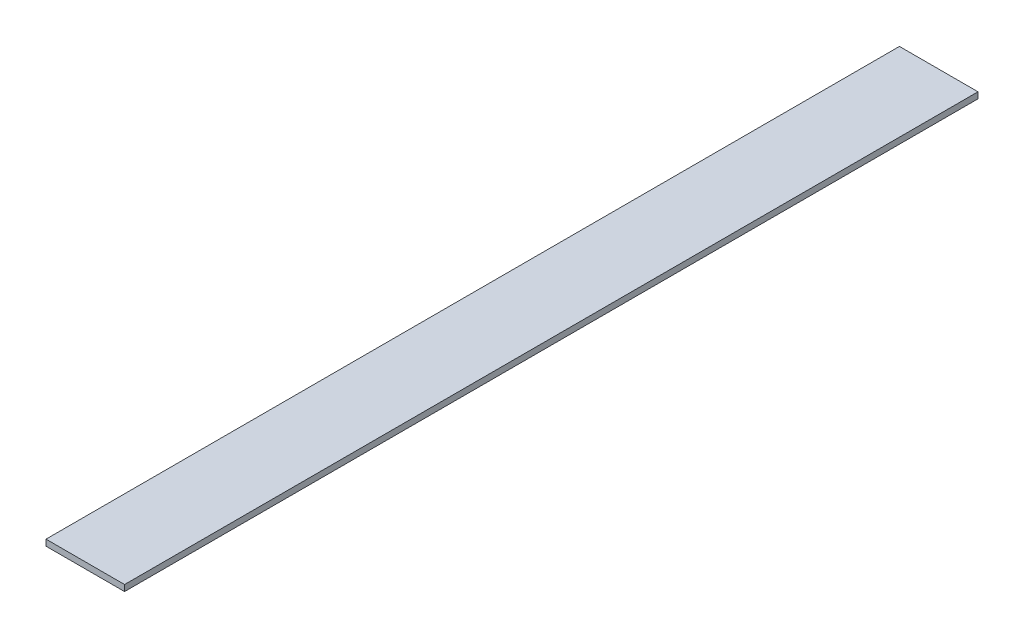
SolidWorks part; units mm, degrees
material "Plywood"
ref_plane "Front Plane" through (0, 0, 0) normal (0, 0, 1) x (1, 0, 0)
ref_plane "Top Plane" through (0, 0, 0) normal (0, 1, 0) x (1, 0, 0)
ref_plane "Right Plane" through (0, 0, 0) normal (1, 0, 0) x (0, 0, -1)
sketch "Sketch1" plane through (0, 0, 0) normal (0, 0, 1) x (1, 0, 0)
  line L1 (0, 0) -> (40.64, 0)
  line L2 (0, 0) -> (0, 3.175)
  line L3 (0, 3.175) -> (40.64, 3.175)
  line L4 (40.64, 0) -> (40.64, 3.175)
  dimension "D1" = 40.64
  dimension "D2" = 3.175
extrude "Boss-Extrude1" add sketch "Sketch1" along normal blind 441.452
